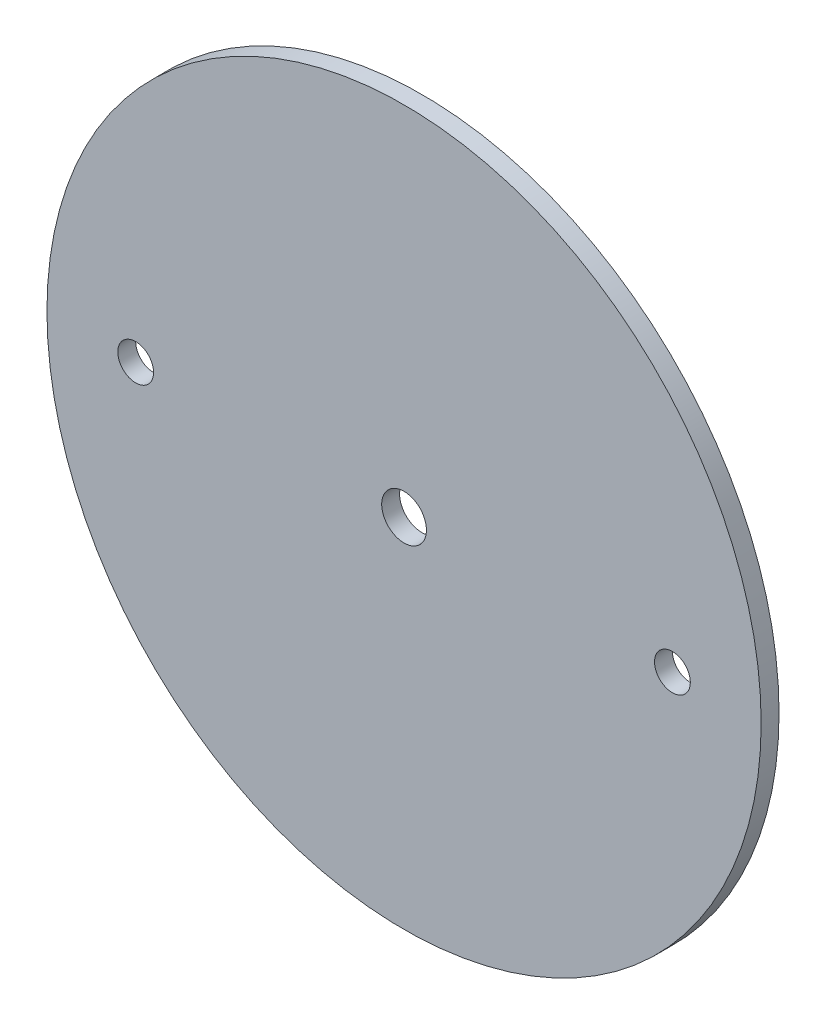
SolidWorks part; units mm, degrees
ref_plane "Front Plane" through (0, 0, 0) normal (0, 0, 1) x (1, 0, 0)
ref_plane "Top Plane" through (0, 0, 0) normal (0, 1, 0) x (1, 0, 0)
ref_plane "Right Plane" through (0, 0, 0) normal (1, 0, 0) x (0, 0, -1)
sketch "Sketch1" plane through (0, 0, 0) normal (0, 0, 1) x (1, 0, 0)
  circle A0 centre (0, 0) radius 63.373
  dimension "D1" = 126.746
extrude "Boss-Extrude1" add sketch "Sketch1" along normal mid plane 3.175
sketch "Sketch2" plane through (0, 0, 1.5875) normal (0, 0, 1) x (1, 0, 0)
  line L0 (-1000, 0) -> (49000, 0) construction
  line L1 (0, -1000) -> (0, 49000) construction
  point P4 (47.625, 0)
  point P5 (-47.625, 0)
  dimension "D2" = 95.25
  dimension "D1" = 47.625
hole_wizard "1/4 (0.25) Diameter Hole1" positions "Sketch2" profile "Sketch3" hole size "1/4" standard "ANSI Inch" end condition through all
sketch "Sketch3" plane through (-47.625, 0, 1.5875) normal (1, 0, 0) x (0, -1, 0)
  line L0 (0, 0) -> (0, 3.175)
  line L1 (0, 3.175) -> (3.175, 3.175)
  line L2 (3.175, 3.175) -> (3.175, 0)
  line L5 (3.175, 0) -> (0, 0)
  line L11 (0, -6.35) -> (0, 107.95) construction
  dimension "Thru Hole Dia." = 6.35
  dimension "Thru Hole Depth" = 3.175
sketch "Sketch4" plane through (0, 0, 1.5875) normal (0, 0, 1) x (1, 0, 0)
  point P0 (0, 0)
hole_wizard "5/16 (0.3125) Diameter Hole1" positions "Sketch4" profile "Sketch5" hole size "5/16" standard "ANSI Inch"
sketch "Sketch5" plane through (0, 0, 1.5875) normal (1, 0, 0) x (0, -1, 0)
  line L0 (0, 0) -> (0, 3.302)
  line L1 (0, 3.302) -> (3.9687, 3.302)
  line L2 (3.9687, 3.302) -> (3.9688, 0)
  line L5 (3.9688, 0) -> (0, 0)
  line L10 (0, 3.302) -> (-3.9688, 3.302) construction
  line L11 (0, -6.35) -> (0, 107.95) construction
  dimension "Hole Dia." = 7.9375
  dimension "Hole Depth" = 3.302
  dimension "Drill Angle" = 180
equation "\"AIRFRAME_OD\"= 5.15in"
equation "\"AIRFRAME_ID\"= 4.99in"
equation "\"FLAT_T\"= 0.125in"
equation "\"NOSE_EXP_L\"= 27in"
equation "\"NOSE_SHOULDER_L\"= 5in"
equation "\"MAIN_L\"= 30in"
equation "\"RECO_COUP_L\"= 10in"
equation "\"RECO_SWITCH_L\"= 2in"
equation "\"DROGUE_L\"= 20in"
equation "\"ATS_FORE_COUP_L\"= 5.5in"
equation "\"ATS_AFT_COUP_L\"= 4.5in"
equation "\"LOWER_L\"= 30in"
equation "\"FIN_N\"= 4"
equation "\"CR_AFT_X\"= 0.5in"
equation "\"CR_FORE_X\"= 9.25in"
equation "\"FIN_ROOT\"= 8in"
equation "\"FIN_X\"= 0.75in"
equation "\"MOTOR_OD\"= 3.091in"
equation "\"MOTOR_ID\"= 3.00in"
equation "\"COUPLER_OD\"= 4.998in"
equation "\"COUPLER_ID\"= 4.85in"
equation "\"D1@Sketch1\"=\"AIRFRAME_ID\""
equation "\"D1@Boss-Extrude1\"=\"FLAT_T\""
equation "\"RECO_ROD_X\"= 3.5in"
equation "\"ATS_ROD_X\"= 3.75in"
equation "\"D2@Sketch2\"=\"ATS_ROD_X\""
equation "\"MOTOR_L\"= 14in"
equation "\"MOTOR_LOWER_X\"= 2in"
equation "\"D1@Sketch2\"=\"ATS_ROD_X\"/2"
